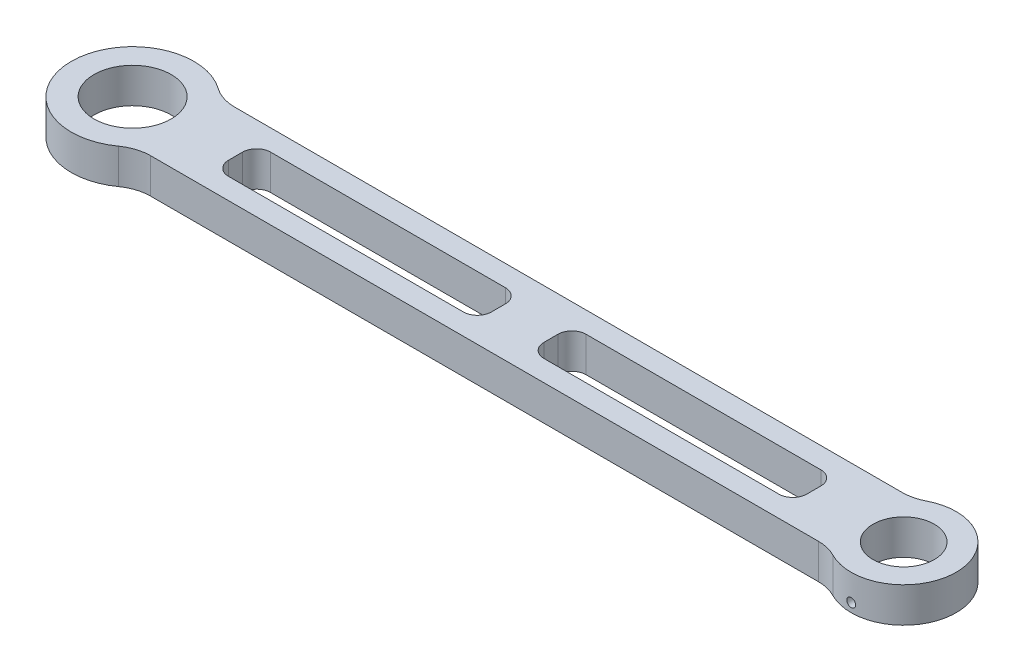
SolidWorks part; units mm, degrees
material "Acrylic (Medium-high impact)"
ref_plane "Front Plane" through (0, 0, 0) normal (0, 0, 1) x (1, 0, 0)
ref_plane "Top Plane" through (0, 0, 0) normal (0, 1, 0) x (1, 0, 0)
ref_plane "Right Plane" through (0, 0, 0) normal (1, 0, 0) x (0, 0, -1)
sketch "Sketch1" plane through (0, 0, 0) normal (0, 1, 0) x (1, 0, 0)
  line L0 (-36.9974, 0) -> (35.0826, 0) construction
  line L1 (12.7377, 12) -> (211, 12)
  line L2 (12.7377, -12) -> (211, -12)
  line L3 (111.8689, 12) -> (111.8689, -12) construction
  line L4 (29.3689, 6) -> (104.3689, 6)
  line L5 (29.3689, 6) -> (29.3689, -6)
  line L6 (29.3689, -6) -> (104.3689, -6)
  line L7 (104.3689, 6) -> (104.3689, -6)
  line L8 (29.3689, 6) -> (104.3689, -6) construction
  line L9 (29.3689, -6) -> (104.3689, 6) construction
  line L10 (194.3689, -6) -> (119.3689, 6) construction
  line L11 (194.3689, 6) -> (119.3689, -6) construction
  line L12 (119.3689, 6) -> (119.3689, -6)
  line L13 (194.3689, -6) -> (119.3689, -6)
  line L14 (194.3689, 6) -> (194.3689, -6)
  line L15 (194.3689, 6) -> (119.3689, 6)
  circle A0 centre (0, 0) radius 17.5
  circle A1 centre (220, 0) radius 15
  circle A2 centre (220, 0) radius 8.75
  circle A3 centre (0, 0) radius 11
  point P13 (66.8689, 0)
  point P24 (156.8689, 0)
  dimension "D2" = 22
  dimension "D3" = 35
  dimension "D8" = 17.5
  dimension "D9" = 30
  dimension "D1" = 220
  dimension "D4" = 12
  dimension "D5" = 12
  dimension "D6" = 75
  dimension "D7" = 45
extrude "Boss-Extrude1" add sketch "Sketch1" along normal blind 10 contours A1 L1 A0 L2 L4 L7 L6 L5 L15 L14 L13 L12 | A0 A3 | A1 A2
fillet "Fillet1" radius 4 8 edges at (104.3689, 5, -6) (194.3689, 5, 6) (194.3689, 5, -6) (119.3689, 5, 6) (119.3689, 5, -6) (29.3689, 5, 6) (29.3689, 5, -6) (104.3689, 5, 6)
fillet "Fillet2" radius 12 4 edges at (211, 5, 12) (211, 5, -12) (12.7377, 5, -12) (12.7377, 5, 12)
sketch "Sketch2" plane through (0, 0, 12) normal (0, 0, 1) x (1, 0, 0)
  line L0 (220, 2.5) -> (220, 10) construction
  line L1 (228.75, 10) -> (211.25, 10) construction
  circle A0 centre (220, 2.5) radius 1.25
  dimension "D1" = 2.5
  dimension "D2" = 2.5
extrude "Cut-Extrude1" cut sketch "Sketch2" against normal mid plane 18
